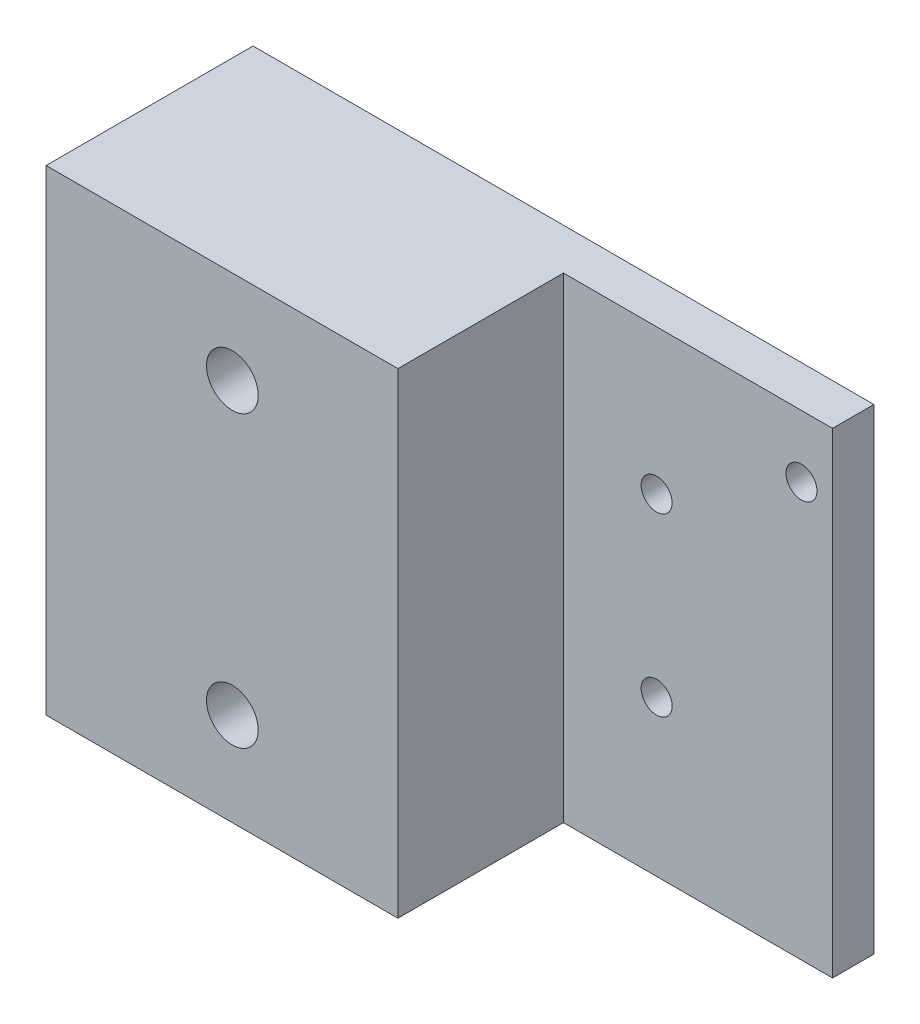
SolidWorks part; units mm, degrees
material "4032-T6"
ref_plane "Plano frontal" through (0, 0, 0) normal (0, 0, 1) x (1, 0, 0)
ref_plane "Plano superior" through (0, 0, 0) normal (0, 1, 0) x (1, 0, 0)
ref_plane "Plano direito" through (0, 0, 0) normal (1, 0, 0) x (0, 0, -1)
sketch "Esboço1" plane through (0, 0, 0) normal (0, 0, 1) x (1, 0, 0)
  line L1 (-30, 23) -> (30, 23)
  line L2 (-30, 23) -> (-30, -23)
  line L3 (-30, -23) -> (30, -23)
  line L4 (30, 23) -> (30, -23)
  line L5 (-30, 23) -> (30, -23) construction
  line L6 (-30, -23) -> (30, 23) construction
  point P0 (0, 0)
  dimension "D1" = 46
  dimension "D2" = 60
extrude "Ressalto-extrusão1" add sketch "Esboço1" along normal blind 20
sketch "Esboço2" plane through (0, 0, 20) normal (0, 0, 1) x (1, 0, 0)
  line L0 (30, 23) -> (-30, 23) construction
  line L1 (30, -23) -> (4, -23)
  line L2 (30, -23) -> (30, 23)
  line L3 (30, 23) -> (4, 23)
  line L4 (4, -23) -> (4, 23)
  dimension "D1" = 26
extrude "Corte-extrusão1" cut sketch "Esboço2" against normal blind 16
sketch "Esboço3" plane through (0, 0, 20) normal (0, 0, 1) x (1, 0, 0)
  line L2 (4, 23) -> (-30, 23) construction
  line L4 (3, 23) -> (-34, 23)
  line L5 (3, 23) -> (3, -23)
  line L6 (3, -23) -> (-34, -23)
  line L7 (-34, 23) -> (-34, -23)
  dimension "D2" = 46
  dimension "D3" = 37
extrude "Ressalto-extrusão2" [suppressed] add sketch "Esboço3" along normal blind 12
sketch "Esboço4" [suppressed] plane through (0, 0, 32) normal (0, 0, 1) x (1, 0, 0)
  line L0 (-34, -23) -> (3, -23) construction
  line L10 (-30, 23) -> (-30, -23)
  line L12 (3, 23) -> (-34, 23) construction
  line L14 (-18, 23) -> (-30, 23)
  line L16 (-30, -23) -> (-18, -23)
  line L17 (-18, 23) -> (-18, -23)
  line L19 (-6, 23) -> (3, 23)
  line L20 (-6, 23) -> (-6, -23)
  line L21 (-6, -23) -> (3, -23)
  line L22 (3, 23) -> (3, -23)
  dimension "D1" = 9
  dimension "D2" = 12
  dimension "D3" = 12
extrude "Corte-extrusão2" [suppressed] cut sketch "Esboço4" against normal blind 9
sketch "Esboço5" plane through (0, 0, 4) normal (0, 0, 1) x (1, 0, 0)
  line L0 (30, -23) -> (30, 23) construction
  line L1 (30, 23) -> (4, 23) construction
  circle A0 centre (13, 9) radius 1.5
  circle A1 centre (13, -8) radius 1.5
  circle A2 centre (27, 17) radius 1.5
  dimension "D1" = 17
  dimension "D2" = 17
  dimension "D3" = 17
  dimension "D4" = 14
  dimension "D5" = 6
  dimension "D6" = 3
extrude "Corte-extrusão3" cut sketch "Esboço5" against normal through all
sketch "Esboço6" [suppressed] plane through (0, 0, 32) normal (0, 0, 1) x (1, 0, 0)
  line L0 (-18, -23) -> (-6, -23) construction
  line L1 (-18, -23) -> (-18, 23) construction
  circle A0 centre (-12, -14) radius 2.5
  circle A1 centre (-12, 14) radius 2.5
  dimension "D1" = 28
  dimension "D2" = 9
  dimension "D3" = 6
  dimension "D4" = 6
extrude "Corte-extrusão4" [suppressed] cut sketch "Esboço6" against normal blind 9
sketch "Esboço8" plane through (0, 0, 20) normal (0, 0, 1) x (1, 0, 0)
  line L0 (4, 23) -> (-30, 23) construction
  line L1 (-30, 23) -> (-30, -23) construction
  circle A0 centre (-12, -14) radius 2.5
  circle A1 centre (-12, 14) radius 2.5
  dimension "D1" = 28
  dimension "D2" = 9
  dimension "D3" = 18
  dimension "D4" = 18
extrude "Corte-extrusão5" cut sketch "Esboço8" against normal through all
sketch "Esboço9" plane through (0, 0, 0) normal (0, 0, -1) x (-1, 0, 0)
  circle A0 centre (12, -14) radius 5
  circle A1 centre (12, 14.0826) radius 5
extrude "Corte-extrusão6" cut sketch "Esboço9" against normal blind 7
